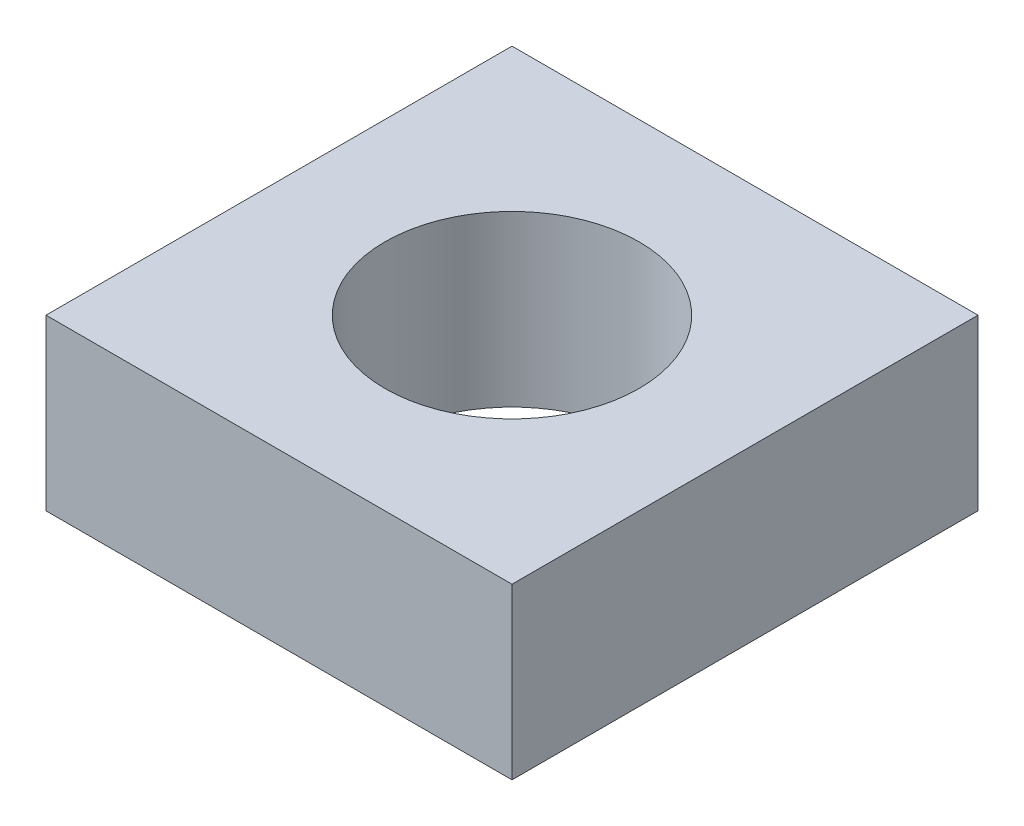
SolidWorks part; units mm, degrees
ref_plane "前视基准面" through (0, 0, 0) normal (0, 0, 1) x (1, 0, 0)
ref_plane "上视基准面" through (0, 0, 0) normal (0, 1, 0) x (1, 0, 0)
ref_plane "右视基准面" through (0, 0, 0) normal (1, 0, 0) x (0, 0, -1)
sketch "草图1" plane through (0, 0, 0) normal (0, 1, 0) x (1, 0, 0)
  line L1 (-2.75, 2.75) -> (2.75, 2.75)
  line L2 (-2.75, 2.75) -> (-2.75, -2.75)
  line L3 (-2.75, -2.75) -> (2.75, -2.75)
  line L4 (2.75, 2.75) -> (2.75, -2.75)
  line L5 (-2.75, 2.75) -> (2.75, -2.75) construction
  line L6 (-2.75, -2.75) -> (2.75, 2.75) construction
  point P0 (0, 0)
  dimension "D1" = 5.5
  dimension "D2" = 5.5
extrude "凸台-拉伸1" add sketch "草图1" along normal blind 2
sketch "草图2" plane through (0, 2, 0) normal (0, 1, 0) x (1, 0, 0)
  circle A0 centre (0, 0) radius 1.5
  dimension "D1" = 3
extrude "切除-拉伸1" cut sketch "草图2" against normal through all
